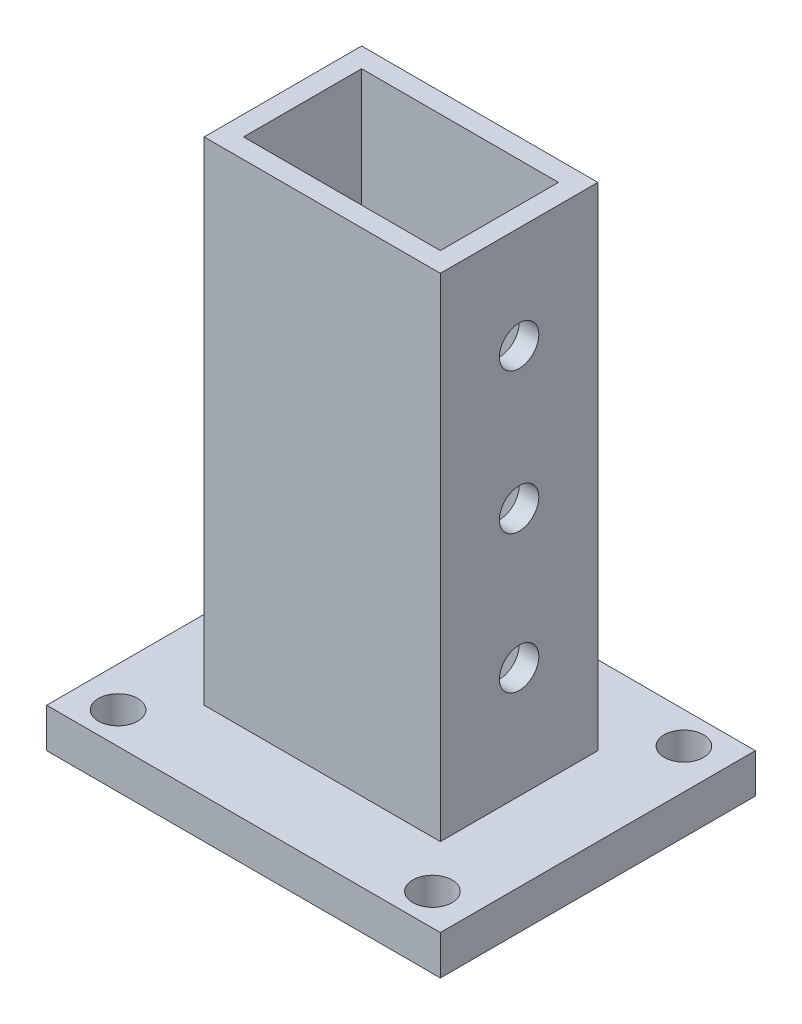
SolidWorks part; units mm, degrees
ref_plane "Płaszczyzna przednia" through (0, 0, 0) normal (0, 0, 1) x (1, 0, 0)
ref_plane "Płaszczyzna górna" through (0, 0, 0) normal (0, 1, 0) x (1, 0, 0)
ref_plane "Płaszczyzna prawa" through (0, 0, 0) normal (1, 0, 0) x (0, 0, -1)
sketch "Szkic1" plane through (0, 0, 0) normal (0, 1, 0) x (1, 0, 0)
  line L1 (50, 40) -> (-50, 40)
  line L2 (50, 40) -> (50, -40)
  line L3 (50, -40) -> (-50, -40)
  line L4 (-50, 40) -> (-50, -40)
  line L5 (50, 40) -> (-50, -40) construction
  line L6 (50, -40) -> (-50, 40) construction
  circle A0 centre (-39.9187, 31.935) radius 5
  circle A1 centre (39.9187, 31.935) radius 5
  circle A2 centre (39.9187, -31.935) radius 5
  circle A3 centre (-39.9187, -31.935) radius 5
  point P0 (0, 0)
  dimension "D3" = 10
  dimension "D4" = 10
  dimension "D5" = 10
  dimension "D6" = 10
  dimension "D1" = 100
  dimension "D2" = 80
extrude "Dodanie-wyciągnięcie1" add sketch "Szkic1" along normal blind 10
sketch "Szkic2" plane through (0, 10, 0) normal (0, 1, 0) x (1, 0, 0)
  line L1 (-25, -15) -> (25, -15)
  line L2 (-25, -15) -> (-25, 15)
  line L3 (-25, 15) -> (25, 15)
  line L4 (25, -15) -> (25, 15)
  line L5 (-25, -15) -> (25, 15) construction
  line L6 (-25, 15) -> (25, -15) construction
  point P0 (0, 0)
  dimension "D1" = 50
  dimension "D2" = 30
extrude "Wyciągnięcie-cienka ścianka1" add sketch "Szkic2" along normal blind 125 thin
sketch "Szkic3" plane through (-30, 0, 0) normal (-1, 0, 0) x (0, 0, 1)
  circle A0 centre (0, 38.2291) radius 5
  circle A1 centre (0, 73.2808) radius 5
  circle A2 centre (0, 109.0665) radius 5
  dimension "D1" = 10
extrude "Wytnij-wyciągnięcie1" cut sketch "Szkic3" against normal blind 125
